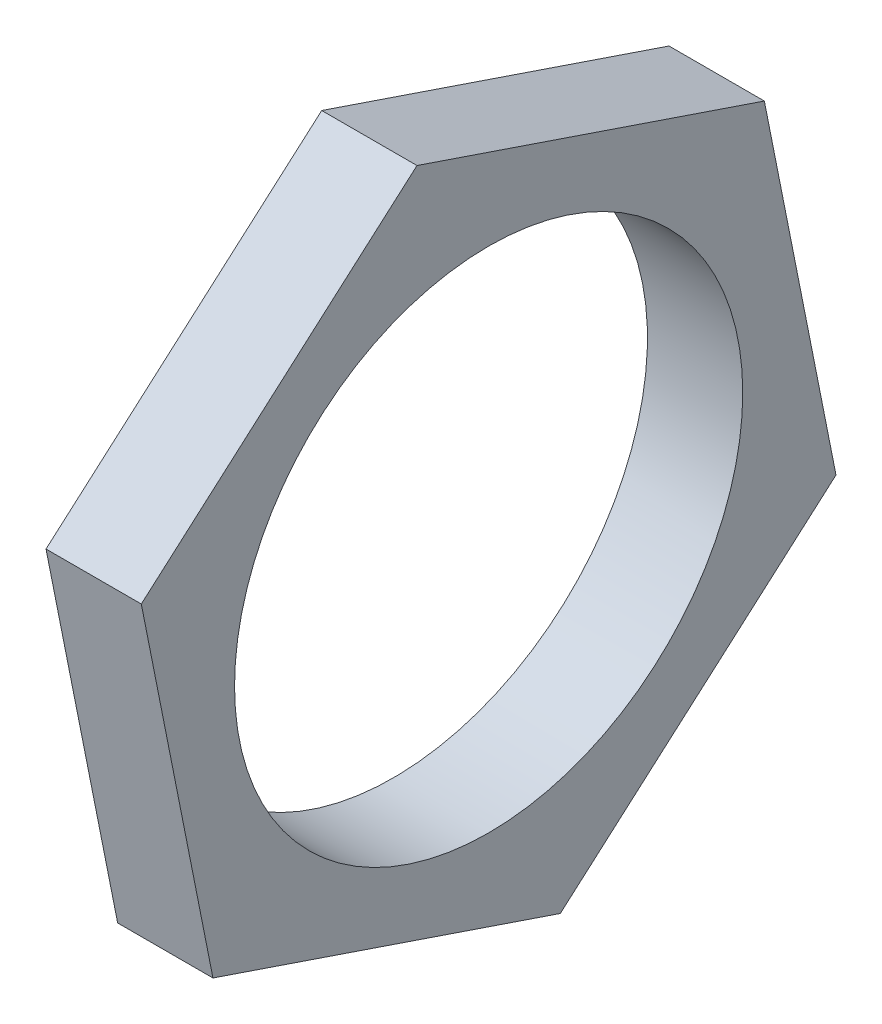
SolidWorks part; units mm, degrees
ref_plane "Front Plane" through (0, 0, 0) normal (0, 0, 1) x (1, 0, 0)
ref_plane "Top Plane" through (0, 0, 0) normal (0, 1, 0) x (1, 0, 0)
ref_plane "Right Plane" through (0, 0, 0) normal (1, 0, 0) x (0, 0, -1)
sketch "Sketch2" plane through (0, 0, 0) normal (1, 0, 0) x (0, 0, -1)
  line L1 (8.6795, 7.6158) -> (-2.2557, 11.3245)
  line L2 (-2.2557, 11.3245) -> (-10.9352, 3.7088)
  line L3 (-10.9352, 3.7088) -> (-8.6795, -7.6158)
  line L4 (-8.6795, -7.6158) -> (2.2557, -11.3245)
  line L5 (2.2557, -11.3245) -> (10.9352, -3.7088)
  line L6 (10.9352, -3.7088) -> (8.6795, 7.6158)
  circle A0 centre (0, 0) radius 10 construction
  dimension "D1" = 20
extrude "Boss-Extrude1" add sketch "Sketch2" along normal blind 3
sketch "Sketch3" plane through (0, 0, 0) normal (-1, 0, 0) x (0, 0, 1)
  circle A0 centre (0, 0) radius 8
  dimension "D1" = 16
extrude "Cut-Extrude1" cut sketch "Sketch3" against normal up to next
